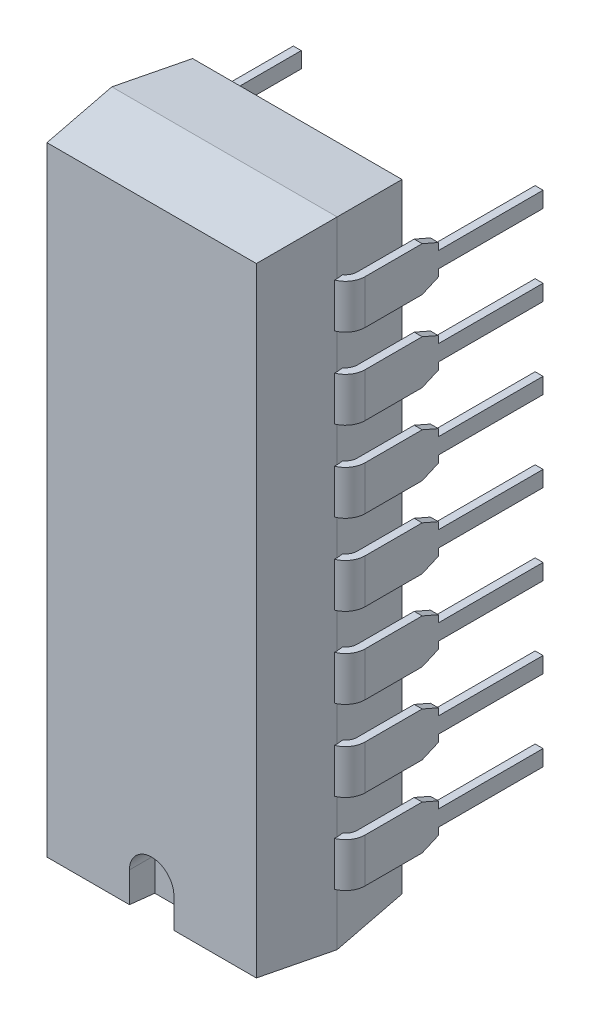
SolidWorks part; units mm, degrees
ref_plane "Front Plane" through (0, 0, 0) normal (0, 0, 1) x (1, 0, 0)
ref_plane "Top Plane" through (0, 0, 0) normal (0, 1, 0) x (1, 0, 0)
ref_plane "Right Plane" through (0, 0, 0) normal (1, 0, 0) x (0, 0, -1)
sketch "Sketch1" plane through (0, 0, 0) normal (0, 1, 0) x (1, 0, 0)
  line L0 (-3.3, -5.1) -> (-3.55, -2.805)
  line L1 (-3.55, -2.805) -> (3.55, -2.805) construction
  line L2 (3.55, -2.805) -> (3.3, -5.1)
  line L3 (3.3, -5.1) -> (-3.3, -5.1)
  line L4 (-3.55, -2.805) -> (-3.3, -0.51)
  line L5 (-3.3, -0.51) -> (3.3, -0.51)
  line L6 (3.3, -0.51) -> (3.55, -2.805)
  line L7 (0, 0) -> (3.3, 0) construction
  line L8 (0, -0.51) -> (0, -5.1) construction
  point P11 (0, -2.805)
  point P12 (0, -5.1)
  point P13 (0, -0.51)
  dimension "D1" = 7.1
  dimension "D2" = 0.51
  dimension "D3" = 5.1
  dimension "D4" = 6.6
extrude "Basic Shape" add sketch "Sketch1" along normal mid plane 20
sketch "Sketch2" plane through (0, 0, 0) normal (1, 0, 0) x (0, 0, -1)
  line L1 (-0.51, -10) -> (-2.805, -10) construction
  line L2 (-0.51, 10) -> (-0.51, -10) construction
  line L3 (-0.51, 10) -> (-0.51, 9.75)
  line L4 (-0.51, 10) -> (-2.805, 10) construction
  line L5 (-0.51, 10) -> (-2.805, 10)
  line L6 (-2.805, 10) -> (-0.51, 9.75)
  line L7 (-0.51, -10) -> (-2.805, -10)
  line L9 (-2.805, -10) -> (-0.51, -9.75)
  line L11 (-0.51, -9.75) -> (-0.51, -10)
  dimension "D1" = 0.25
extrude "Side Profile1" cut sketch "Sketch2" against normal through all and the other way through all
sketch "Sketch3" plane through (0, 0, 0) normal (1, 0, 0) x (0, 0, -1)
  line L0 (-2.805, 10) -> (-5.1, 10) construction
  line L1 (-2.805, 10) -> (-5.1, 10)
  line L2 (-5.1, 10) -> (-5.1, -10) construction
  line L3 (-5.1, 10) -> (-5.1, 9.75)
  line L4 (-2.805, 10) -> (-5.1, 9.75)
  line L5 (-2.805, -10) -> (-5.1, -10) construction
  line L6 (-2.805, -10) -> (-5.1, -10)
  line L7 (-2.805, -10) -> (-5.1, -9.75)
  line L8 (-5.1, -9.75) -> (-5.1, -10)
extrude "Side Profile2" cut sketch "Sketch3" against normal through all and the other way through all
sketch "Sketch4" plane through (0, 0, 5.1) normal (0, 0, 1) x (1, 0, 0)
  line L2 (-0.7, -10) -> (-0.7, -8.8)
  line L3 (0.7, -8.8) -> (0.7, -10)
  line L4 (-3.55, -10) -> (3.55, -10) construction
  line L5 (-0.7, -10) -> (0.7, -10)
  arc A0 (-0.7, -8.8) -> (0.7, -8.8) centre (0, -8.8) cw
  dimension "D1" = 1.2
  dimension "D2" = 1.4
extrude "Location Mark" cut sketch "Sketch4" against normal blind 0.8
sketch "Sketch5" plane through (0, 0, 0) normal (0, 1, 0) x (1, 0, 0)
  line L0 (-3.55, -2.805) -> (3.55, -2.805) construction
  line L1 (0, -2.805) -> (3.31, -2.805)
  line L2 (3.81, -2.305) -> (3.81, 3.3)
  line L3 (3.81, -2.805) -> (-3.81, -2.805) construction
  arc A0 (3.81, -2.305) -> (3.31, -2.805) centre (3.31, -2.305) cw
  point P0 (-3.81, -2.805)
  point P8 (0, -2.805)
  dimension "D3" = 0.5
  dimension "D1" = 7.62
  dimension "D2" = 3.3
sketch "Sketch6" plane through (0, 0, 0) normal (1, 0, 0) x (0, 0, -1)
  line L0 (-2.93, 0.695) -> (-2.68, 0.695)
  line L1 (-2.93, 0.695) -> (-2.93, -0.695)
  line L2 (-2.68, -0.695) -> (-2.93, -0.695)
  line L3 (-2.68, -0.695) -> (-2.68, 0.695)
  line L4 (-2.68, 0.695) -> (-2.93, -0.695) construction
  point P4 (-2.805, 0)
  dimension "D1" = 1.39
  dimension "D2" = 0.25
sweep "Central Pin" add profiles "Sketch6" path "Sketch5"
sketch "Sketch7" plane through (3.685, 0, 0) normal (-1, 0, 0) x (0, 0, 1)
  line L0 (-3.3, -0.695) -> (-3.3, 0.695) construction
  line L1 (2.305, -0.695) -> (-3.3, -0.695) construction
  line L2 (-3.3, -0.25) -> (-3.3, 0.25) construction
  line L3 (-3.3, -0.25) -> (0, -0.25)
  line L4 (50, 0) -> (-50, 0) construction
  line L5 (-3.3, 0.25) -> (0, 0.25)
  line L6 (0, 0.25) -> (0, 0.4725)
  line L7 (0, -0.25) -> (0, -0.4725)
  line L8 (2.305, 0.695) -> (-3.3, 0.695) construction
  line L9 (0.51, 0.695) -> (-3.3, 0.695)
  line L10 (2.305, -0.695) -> (-3.3, -0.695) construction
  line L11 (0.51, -0.695) -> (-3.3, -0.695)
  line L12 (-3.3, -0.25) -> (-3.3, -0.695)
  line L13 (-3.3, 0.695) -> (-3.3, 0.25)
  line L14 (0, -0.4725) -> (0.51, -0.695)
  line L16 (0, 0.4725) -> (0.51, 0.695)
  line L17 (2.305, 0.695) -> (-3.3, 0.695) construction
  line L18 (0.51, 9.75) -> (0.51, -9.75) construction
  point P6 (-3.3, 0)
  point P10 (-3.3, 0.4725)
  dimension "D1" = 0.5
extrude "Pin Relief" cut sketch "Sketch7" against normal through all
mirror "Opp Pin" about plane through (0, 0, 0) normal (1, 0, 0) of "Pin Relief", "Central Pin"
pattern_linear "Upper Pins" count 4 spacing 2.54 along (0, -1, 0) of "Central Pin", "Opp Pin", "Pin Relief"
pattern_linear "Lower Pins" count 4 spacing 2.54 along (0, 1, 0) of "Pin Relief", "Opp Pin", "Central Pin"
sketch "Component_Outline" plane through (0, 0, 0) normal (0, 0, 1) x (1, 0, 0)
  line L0 (3.55, 10) -> (3.55, 8.315)
  line L1 (3.55, 8.315) -> (3.935, 8.315)
  line L2 (3.935, 8.315) -> (3.935, 6.925)
  line L3 (3.935, 6.925) -> (3.55, 6.925)
  line L4 (3.55, 6.925) -> (3.55, 5.775)
  line L5 (3.55, 5.775) -> (3.935, 5.775)
  line L6 (3.935, 5.775) -> (3.935, 4.385)
  line L7 (3.935, 4.385) -> (3.55, 4.385)
  line L8 (3.55, 4.385) -> (3.55, 3.235)
  line L9 (3.55, 3.235) -> (3.935, 3.235)
  line L10 (3.935, 3.235) -> (3.935, 1.845)
  line L11 (3.935, 1.845) -> (3.5287, 1.845)
  line L12 (3.5287, 1.845) -> (3.55, 0.695)
  line L13 (3.55, 0.695) -> (3.935, 0.695)
  line L14 (3.935, 0.695) -> (3.935, -0.695)
  line L15 (3.935, -0.695) -> (3.55, -0.695)
  line L16 (3.55, -0.695) -> (3.55, -1.845)
  line L17 (3.55, -1.845) -> (3.935, -1.845)
  line L18 (3.935, -1.845) -> (3.935, -3.235)
  line L19 (3.935, -3.235) -> (3.55, -3.235)
  line L20 (3.55, -3.235) -> (3.55, -4.385)
  line L21 (3.55, -4.385) -> (3.935, -4.385)
  line L22 (3.935, -4.385) -> (3.935, -5.775)
  line L23 (3.935, -5.775) -> (3.55, -5.775)
  line L24 (3.55, -5.775) -> (3.55, -6.925)
  line L25 (3.55, -6.925) -> (3.935, -6.925)
  line L26 (3.935, -6.925) -> (3.935, -8.315)
  line L27 (3.935, -8.315) -> (3.55, -8.315)
  line L28 (3.55, -8.315) -> (3.55, -10)
  line L29 (0, 10) -> (0, -10) construction
  line L30 (-3.55, 10) -> (3.55, 10) construction
  line L31 (-3.55, -10) -> (3.55, -10) construction
  line L32 (-3.55, -8.315) -> (-3.55, -10)
  line L33 (-3.935, -8.315) -> (-3.55, -8.315)
  line L34 (-3.935, -6.925) -> (-3.935, -8.315)
  line L35 (-3.55, -6.925) -> (-3.935, -6.925)
  line L36 (-3.55, -5.775) -> (-3.55, -6.925)
  line L37 (-3.935, -5.775) -> (-3.55, -5.775)
  line L38 (-3.935, -4.385) -> (-3.935, -5.775)
  line L39 (-3.55, -4.385) -> (-3.935, -4.385)
  line L40 (-3.55, -3.235) -> (-3.55, -4.385)
  line L41 (-3.935, -3.235) -> (-3.55, -3.235)
  line L42 (-3.935, -1.845) -> (-3.935, -3.235)
  line L43 (-3.55, -1.845) -> (-3.935, -1.845)
  line L44 (-3.55, -0.695) -> (-3.55, -1.845)
  line L45 (-3.935, -0.695) -> (-3.55, -0.695)
  line L46 (-3.935, 0.695) -> (-3.935, -0.695)
  line L47 (-3.55, 0.695) -> (-3.935, 0.695)
  line L48 (-3.5287, 1.845) -> (-3.55, 0.695)
  line L49 (-3.935, 1.845) -> (-3.5287, 1.845)
  line L50 (-3.935, 3.235) -> (-3.935, 1.845)
  line L51 (-3.55, 3.235) -> (-3.935, 3.235)
  line L52 (-3.55, 4.385) -> (-3.55, 3.235)
  line L53 (-3.935, 4.385) -> (-3.55, 4.385)
  line L54 (-3.935, 5.775) -> (-3.935, 4.385)
  line L55 (-3.55, 5.775) -> (-3.935, 5.775)
  line L56 (-3.55, 6.925) -> (-3.55, 5.775)
  line L57 (-3.935, 6.925) -> (-3.55, 6.925)
  line L58 (-3.935, 8.315) -> (-3.935, 6.925)
  line L59 (-3.55, 8.315) -> (-3.935, 8.315)
  line L60 (-3.55, 10) -> (-3.55, 8.315)
  line L61 (3.55, 10) -> (-3.55, 10)
  line L62 (3.55, -10) -> (-3.55, -10)
  line L63 (3.55, -8.315) -> (3.935, -6.925) construction
  point P96 (3.7425, -7.62)
